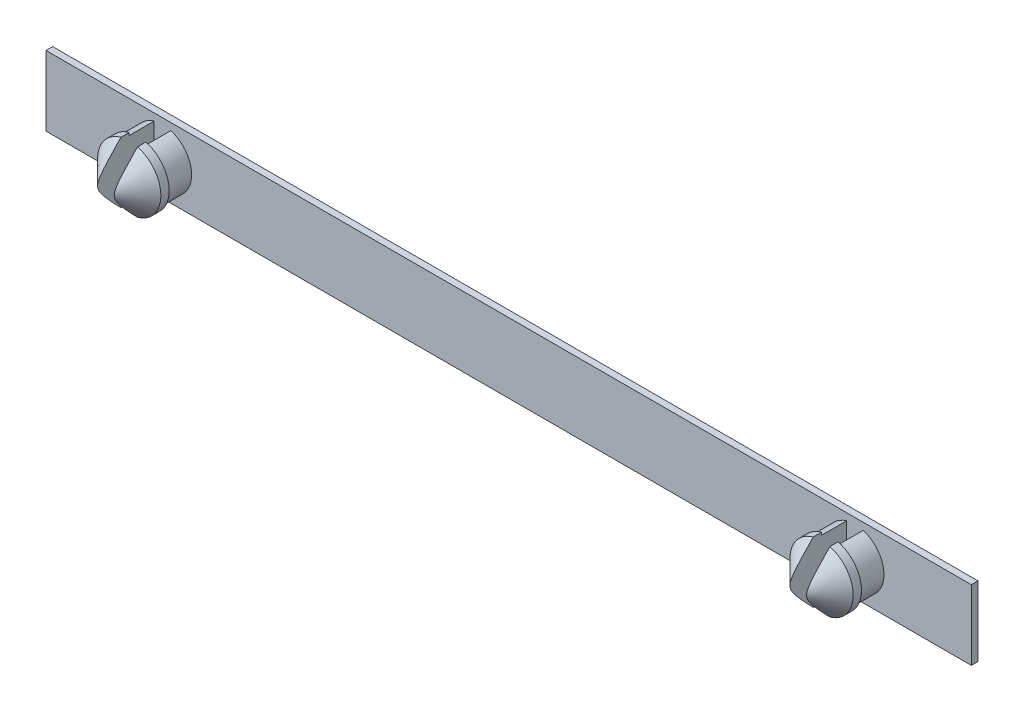
SolidWorks part; units mm, degrees
ref_plane "Přední rovina" through (0, 0, 0) normal (0, 0, 1) x (1, 0, 0)
ref_plane "Horní rovina" through (0, 0, 0) normal (0, 1, 0) x (1, 0, 0)
ref_plane "Pravá rovina" through (0, 0, 0) normal (1, 0, 0) x (0, 0, -1)
sketch "Skica2" plane through (0, 0, 0) normal (0, 0, 1) x (1, 0, 0)
  line L1 (-27.8, 2.1) -> (27.8, 2.1)
  line L2 (-27.8, 2.1) -> (-27.8, -2.1)
  line L3 (-27.8, -2.1) -> (27.8, -2.1)
  line L4 (27.8, 2.1) -> (27.8, -2.1)
  line L5 (-27.8, 2.1) -> (27.8, -2.1) construction
  line L6 (-27.8, -2.1) -> (27.8, 2.1) construction
  point P0 (0, 0)
  point P5 (0, 0)
  dimension "D1" = 4.2
  dimension "D2" = 55.6
  dimension "D7" = 0
extrude "Přidat vysunutím2" add sketch "Skica2" along normal blind 0.4
sketch "Skica3" plane through (0, 0, 0.4) normal (0, 0, 1) x (1, 0, 0)
  line L0 (-27.8, 2.1) -> (-27.8, -2.1) construction
  line L1 (27.8, -2.1) -> (27.8, 2.1) construction
  line L2 (27.8, 2.1) -> (-27.8, 2.1) construction
  line L3 (-27.8, -2.1) -> (27.8, -2.1) construction
  circle A0 centre (-20.8, 0) radius 1.75
  circle A1 centre (20.8, 0) radius 1.75
  dimension "D1" = 3.5
  dimension "D3" = 3.5
  dimension "D2" = 7
  dimension "D4" = 7
  dimension "D5" = 2.1
  dimension "D6" = 2.1
extrude "Přidat vysunutím3" add sketch "Skica3" along normal blind 1.5
sketch "Skica5" plane through (0, 0, 1.9) normal (0, 0, 1) x (1, 0, 0)
  circle A0 centre (-20.8, 0) radius 1.9
  circle A1 centre (20.8, 0) radius 1.9
  dimension "D1" = 3.8
  dimension "D2" = 3.8
extrude "Přidat vysunutím5" add sketch "Skica5" along normal blind 2
chamfer "Zkosení2" distance 1.5 angle 45 2 edges at (22.7, 0, 3.9) (-18.9, 0, 3.9)
sketch "Skica7" plane through (0, 0, 3.9) normal (0, 0, 1) x (1, 0, 0)
  line L1 (-20.3, 2.5) -> (-21.3, 2.5)
  line L2 (-20.3, 2.5) -> (-20.3, -2.5)
  line L3 (-20.3, -2.5) -> (-21.3, -2.5)
  line L4 (-21.3, 2.5) -> (-21.3, -2.5)
  line L5 (-20.3, 2.5) -> (-21.3, -2.5) construction
  line L6 (-20.3, -2.5) -> (-21.3, 2.5) construction
  line L7 (20.3, 2.5) -> (21.3, 2.5)
  line L8 (20.3, 2.5) -> (20.3, -2.5)
  line L9 (20.3, -2.5) -> (21.3, -2.5)
  line L10 (21.3, 2.5) -> (21.3, -2.5)
  line L11 (20.3, 2.5) -> (21.3, -2.5) construction
  line L12 (20.3, -2.5) -> (21.3, 2.5) construction
  point P0 (-20.8, 0)
  point P5 (20.8, 0)
  dimension "D1" = 5
  dimension "D2" = 1
  dimension "D3" = 5
  dimension "D4" = 1
extrude "Odebrat vysunutím1" cut sketch "Skica7" against normal blind 3.5
equation "\"1.5.000mm\"=10"
